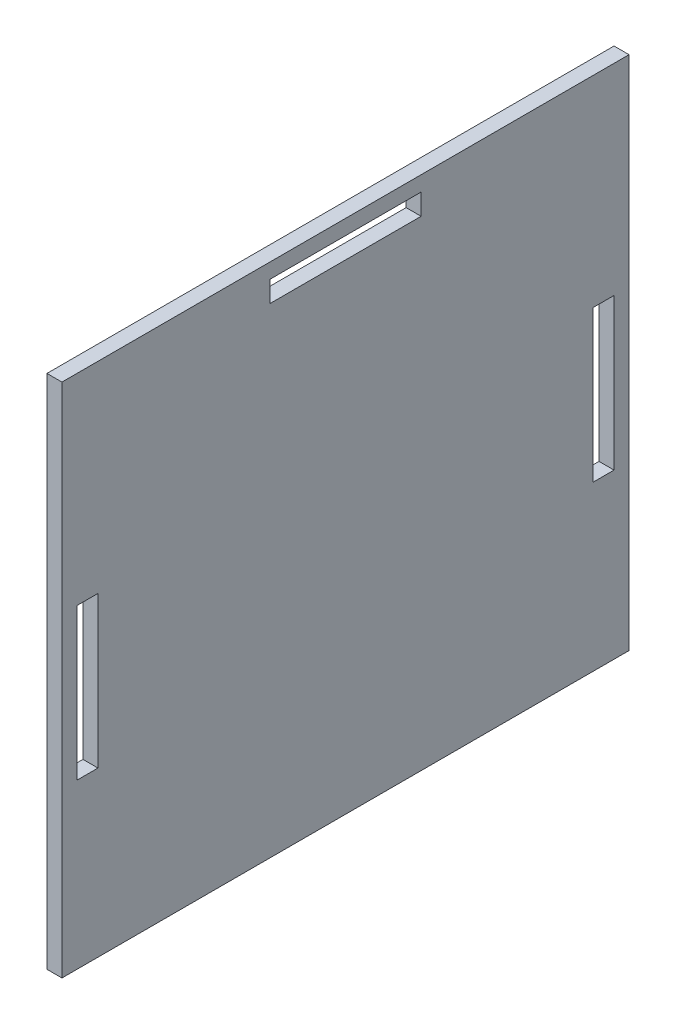
SolidWorks part; units mm, degrees
ref_plane "Front Plane" through (0, 0, 0) normal (0, 0, 1) x (1, 0, 0)
ref_plane "Top Plane" through (0, 0, 0) normal (0, 1, 0) x (1, 0, 0)
ref_plane "Right Plane" through (0, 0, 0) normal (1, 0, 0) x (0, 0, -1)
sketch "Sketch1" plane through (0, 0, 0) normal (1, 0, 0) x (0, 0, -1)
  line L0 (-177, 105) -> (-184, 105)
  line L1 (0, 0) -> (-189, 0)
  line L2 (0, 0) -> (0, 172)
  line L3 (0, 172) -> (-189, 172)
  line L4 (-189, 0) -> (-189, 172)
  line L5 (-94.5, 172) -> (-94.5, 0) construction
  line L6 (0, 86) -> (-189, 86) construction
  line L7 (-119.7, 167) -> (-69.3, 167)
  line L8 (-119.7, 167) -> (-119.7, 160)
  line L9 (-119.7, 160) -> (-69.3, 160)
  line L10 (-69.3, 167) -> (-69.3, 160)
  line L11 (-94.5, 160) -> (-94.5, 167) construction
  line L12 (-119.7, 163.5) -> (-69.3, 163.5) construction
  line L13 (-12, 54.6) -> (-5, 54.6)
  line L14 (-12, 54.6) -> (-12, 105)
  line L15 (-12, 105) -> (-5, 105)
  line L16 (-5, 54.6) -> (-5, 105)
  line L17 (-8.5, 105) -> (-8.5, 54.6) construction
  line L18 (-12, 79.8) -> (-5, 79.8) construction
  line L23 (-184, 54.6) -> (-184, 105)
  line L24 (-177, 54.6) -> (-184, 54.6)
  line L25 (-177, 54.6) -> (-177, 105)
  point P28 (-94.5, 163.5)
  point P85 (-138.7737, 118.4723)
  point P209 (-8.5, 79.8)
  point P236 (-94.5, 86)
  dimension "D1" = 5
  dimension "D2" = 7
  dimension "D3" = 7
  dimension "D4" = 50.4
  dimension "D5" = 50.4
  dimension "D6" = 5
  dimension "D7" = 189
  dimension "D8" = 160
  dimension "D9" = 55
extrude "Boss-Extrude1" add sketch "Sketch1" along normal blind 5 contours L2 L1 L4 L3 | L0 L23 L24 L25 | L8 L7 L10 L9 | L14 L13 L16 L15
